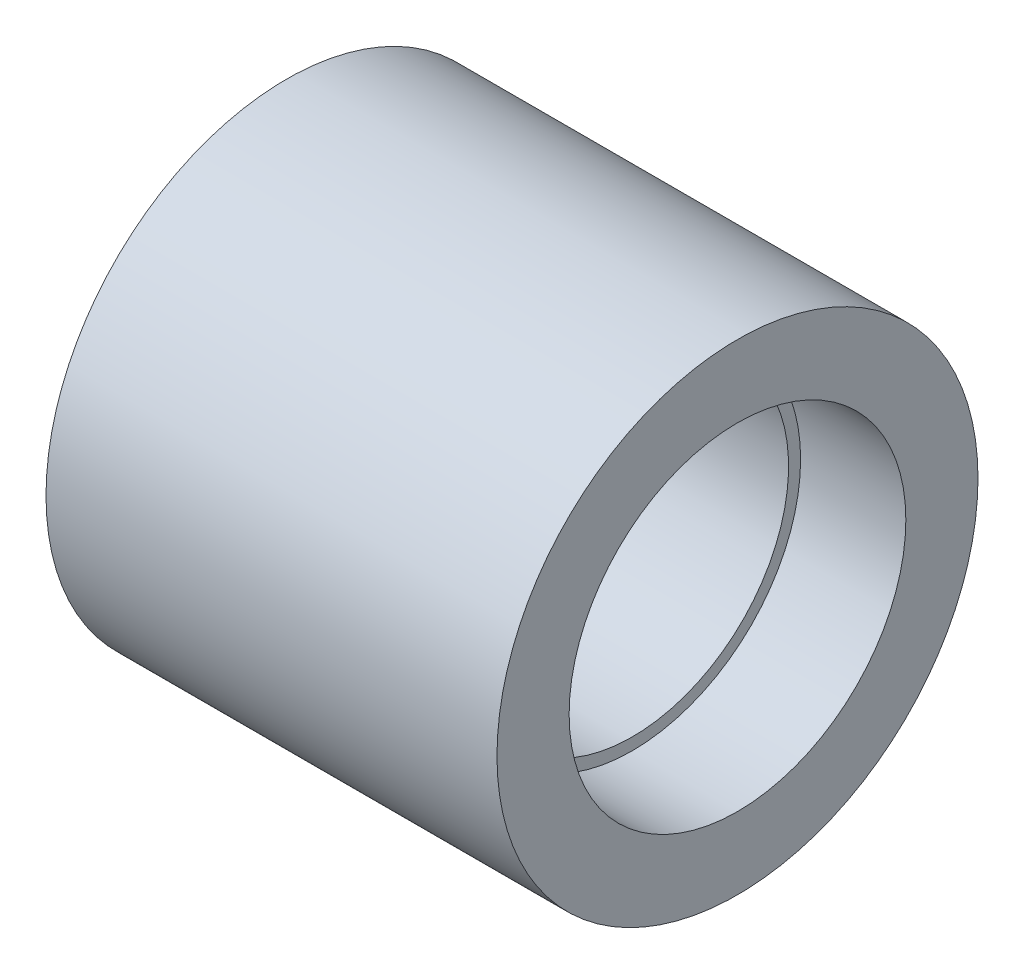
SolidWorks part; units mm, degrees
ref_plane "Front Plane" through (0, 0, 0) normal (0, 0, 1) x (1, 0, 0)
ref_plane "Top Plane" through (0, 0, 0) normal (0, 1, 0) x (1, 0, 0)
ref_plane "Right Plane" through (0, 0, 0) normal (1, 0, 0) x (0, 0, -1)
sketch "Sketch1" plane through (0, 0, 0) normal (0, 0, 1) x (1, 0, 0)
  line L0 (0, 30) -> (0, 106.5061) construction
  line L1 (-1000, 30) -> (49000, 30) construction
  line L2 (-37.5, 70) -> (37.5, 70)
  line L3 (-37.5, 70) -> (-37.5, 58)
  line L4 (-37.5, 58) -> (37.5, 58)
  line L5 (37.5, 70) -> (37.5, 58)
  line L9 (-20, 58) -> (-20, 56)
  line L10 (-20, 56) -> (20, 56)
  line L11 (20, 58) -> (20, 56)
  point P2 (0, 70)
  point P3 (0, 93)
  point P9 (0, 58)
  point P13 (0, 56)
  dimension "D1" = 40
  dimension "D2" = 28
  dimension "D3" = 75
  dimension "D4" = 40
  dimension "D5" = 26
revolve "Revolve1" add sketch "Sketch1" angle 360 about L1
